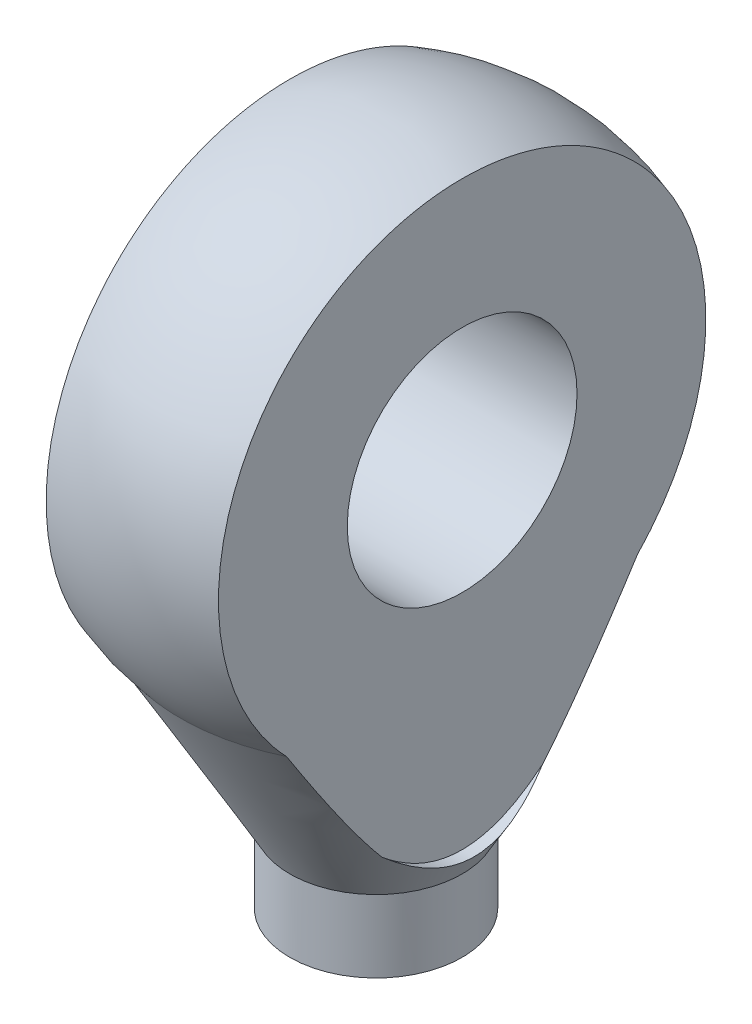
SolidWorks part; units mm, degrees
ref_plane "Płaszczyzna przednia" through (0, 0, 0) normal (0, 0, 1) x (1, 0, 0)
ref_plane "Płaszczyzna górna" through (0, 0, 0) normal (0, 1, 0) x (1, 0, 0)
ref_plane "Płaszczyzna prawa" through (0, 0, 0) normal (1, 0, 0) x (0, 0, -1)
sketch "Szkic1" plane through (0, 0, 0) normal (0, 0, 1) x (1, 0, 0)
  line L0 (0, 0) -> (0, 67.6259) construction
  line L1 (0, 0) -> (-2, 0)
  line L2 (-2, 0) -> (-2, 47.516)
  line L3 (-2, 47.516) -> (-4, 47.516)
  line L4 (-4, 47.516) -> (-4, 52.516)
  line L5 (-4, 52.516) -> (-3, 52.516)
  line L6 (-3, 52.516) -> (-3, 72.516)
  line L7 (0, 94) -> (0, 76) construction
  line L8 (-3, 72.516) -> (-6.8112, 79.1172)
  line L9 (0, 94) -> (0, 87.5)
  line L10 (0, 82.5) -> (0, 0)
  arc A0 (0, 94) -> (-6.8112, 79.1172) centre (0, 85) ccw
  arc A1 (0, 87.5) -> (0, 82.5) centre (0, 85) ccw
  point P11 (-4, 50.016)
  dimension "D1" = 18
  dimension "D5" = 5
  dimension "D2" = 4
  dimension "D3" = 8
  dimension "D4" = 6
  dimension "D6" = 30
  dimension "D7" = 85
  dimension "D8" = 5
  dimension "D9" = 20
revolve "Obrót1" add sketch "Szkic1" angle 360 about L10
sketch "Szkic2" plane through (0, 0, 0) normal (0, 1, 0) x (1, 0, 0)
  line L0 (0, 11.7218) -> (0, -11.8125) construction
  line L1 (-9.6119, -9) -> (-4, -9)
  line L2 (9.6119, 9) -> (4, 9)
  line L3 (9.6119, 9) -> (9.6119, -9)
  line L4 (9.6119, -9) -> (4, -9)
  line L5 (4, 9) -> (4, -9)
  line L6 (-4, 9) -> (-4, -9)
  line L7 (-9.6119, 9) -> (-4, 9)
  line L8 (-9.6119, 9) -> (-9.6119, -9)
  point P7 (4, 0)
  dimension "D1" = 18
  dimension "D2" = 4
extrude "Wytnij-wyciągnięcie3" cut sketch "Szkic2" along normal blind 100
sketch "Szkic3" plane through (-4, 0, 0) normal (-1, 0, 0) x (0, 0, 1)
  circle A0 centre (0, 85) radius 4
  dimension "D1" = 8
extrude "Wytnij-wyciągnięcie4" cut sketch "Szkic3" against normal through all
sketch "Szkic4" plane through (-4, 0, 0) normal (-1, 0, 0) x (0, 0, 1)
  arc A6 (6.2707, 78.4576) -> (-6.2707, 78.4576) centre (0, 85) ccw
  arc A8 (6.2707, 78.4576) -> (-6.2707, 78.4576) centre (0, 85) ccw
  spline S3 degree 3 poles (-2429.6957, -1686.3457) (18.6783, 219.2155) (-34.9353, 114.4261) (-4.5633, 76.2156) (-4.1064, 75.6775) (-3.3634, 74.9223) (-3.1068, 74.6807) (-2.5657, 74.2295) (-2.2785, 74.0186) (-1.6741, 73.6585) (-1.3565, 73.509) (-0.6767, 73.2998) (-0.3288, 73.2454) (0.2029, 73.2495) (0.3807, 73.2655) (0.7278, 73.3235) (0.8986, 73.3659) (1.2349, 73.4745) (1.4007, 73.5412) (1.7193, 73.6916) (1.8734, 73.7757) (2.3227, 74.0493) (2.6069, 74.2614) (3.1455, 74.716) (3.399, 74.957) (4.1303, 75.7053) (4.5805, 76.2365) (35.0354, 114.6011) (-16.178, 222.9114) (2361.3861, -1776.3482) knots -8.413049 -8.413049 -8.413049 -8.413049 0.125 0.125 0.25 0.25 0.3125 0.3125 0.375 0.375 0.4375 0.4375 0.5 0.5 0.53125 0.53125 0.5625 0.5625 0.59375 0.59375 0.625 0.625 0.6875 0.6875 0.75 0.75 0.875 0.875 9.534839 9.534839 9.534839 9.534839 only from (-6.2707, 78.4576) to (6.2707, 78.4576)
  spline S4 degree 3 poles (-6.2707, 78.4576) (-5.8602, 77.884) (-5.4398, 77.3183) (-4.5633, 76.2156) (-4.1064, 75.6775) (-3.3634, 74.9223) (-3.1068, 74.6807) (-2.5657, 74.2295) (-2.2785, 74.0186) (-1.6741, 73.6585) (-1.3565, 73.509) (-0.6767, 73.2998) (-0.3288, 73.2454) (0.2029, 73.2495) (0.3807, 73.2655) (0.7278, 73.3235) (0.8986, 73.3659) (1.2349, 73.4745) (1.4007, 73.5412) (1.7193, 73.6916) (1.8734, 73.7757) (2.3227, 74.0493) (2.6069, 74.2614) (3.1455, 74.716) (3.399, 74.957) (4.1303, 75.7053) (4.5805, 76.2365) (5.4472, 77.3283) (5.8637, 77.8889) (6.2707, 78.4576) knots 0 0 0 0 0.125 0.125 0.25 0.25 0.3125 0.3125 0.375 0.375 0.4375 0.4375 0.5 0.5 0.53125 0.53125 0.5625 0.5625 0.59375 0.59375 0.625 0.625 0.6875 0.6875 0.75 0.75 0.875 0.875 1 1 1 1
  dimension "D1" = 1
extrude "Wytnij-wyciągnięcie5" cut sketch "Szkic4" against normal blind 1
mirror "Lustro1" about plane through (0, 0, 0) normal (1, 0, 0) of "Wytnij-wyciągnięcie5"
sketch "Szkic5" plane through (0, 0, 0) normal (0, 1, 0) x (1, 0, 0)
  circle A0 centre (0, 0) radius 4
extrude "Wytnij-wyciągnięcie6" cut sketch "Szkic5" along normal blind 70
